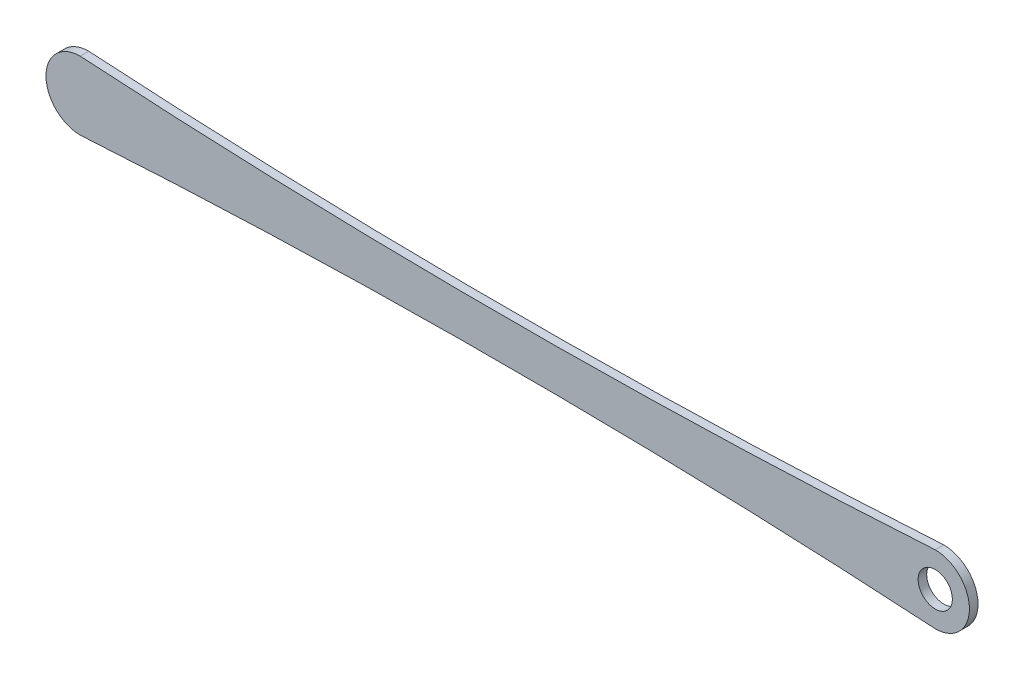
SolidWorks part; units mm, degrees
ref_plane "Front Plane" through (0, 0, 0) normal (0, 0, 1) x (1, 0, 0)
ref_plane "Top Plane" through (0, 0, 0) normal (0, 1, 0) x (1, 0, 0)
ref_plane "Right Plane" through (0, 0, 0) normal (1, 0, 0) x (0, 0, -1)
sketch "Sketch1" plane through (0, 0, 0) normal (0, 0, 1) x (1, 0, 0)
  line L0 (-1250, 0) -> (1250, 0) construction
  line L1 (-1250, -100) -> (1250, -100) construction
  line L3 (-1250, 100) -> (1250, 100) construction
  line L5 (-1250, -100) -> (1250, 100) construction
  line L6 (-1250, 100) -> (1250, -100) construction
  arc A0 (-1250, 100) -> (-1250, -100) centre (-1250, 0) ccw
  arc A1 (1250, -100) -> (1250, 100) centre (1250, 0) ccw
  arc A2 (-1250, 100) -> (1250, 100) centre (0, 20060.8993) ccw
  arc A3 (-1250, -100) -> (1250, -100) centre (0, -20060.8993) cw
  point P0 (0, 0)
  dimension "D6" = 20000
  dimension "D2" = 100
  dimension "D1" = 2500
  dimension "D3" = 200
extrude "Boss-Extrude1" add sketch "Sketch1" along normal blind 25
sketch "Sketch3" plane through (0, 0, 25) normal (0, 0, 1) x (1, 0, 0)
  circle A1 centre (1250, 0) radius 50
  dimension "D2" = 100
  dimension "D1" = 1250
sketch "Sketch2" plane through (0, 0, 0) normal (0, 0, -1) x (1, 0, 0)
  circle A0 centre (-1250, 0) radius 50
  dimension "D2" = 1250
  dimension "D1" = 100
extrude "Boss-Extrude2" add sketch "Sketch2" along normal blind 25
extrude "Cut-Extrude2" cut sketch "Sketch3" against normal blind 25
